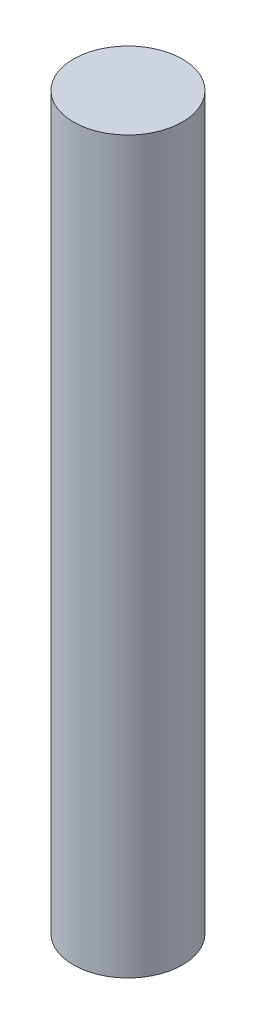
SolidWorks part; units mm, degrees
ref_plane "Front Plane" through (0, 0, 0) normal (0, 0, 1) x (1, 0, 0)
ref_plane "Top Plane" through (0, 0, 0) normal (0, 1, 0) x (1, 0, 0)
ref_plane "Right Plane" through (0, 0, 0) normal (1, 0, 0) x (0, 0, -1)
sketch "Sketch1" plane through (0, 0, 0) normal (0, 1, 0) x (1, 0, 0)
  circle A0 centre (0, 0) radius 3
  dimension "D1" = 6
extrude "Boss-Extrude1" add sketch "Sketch1" along normal blind 40.175
